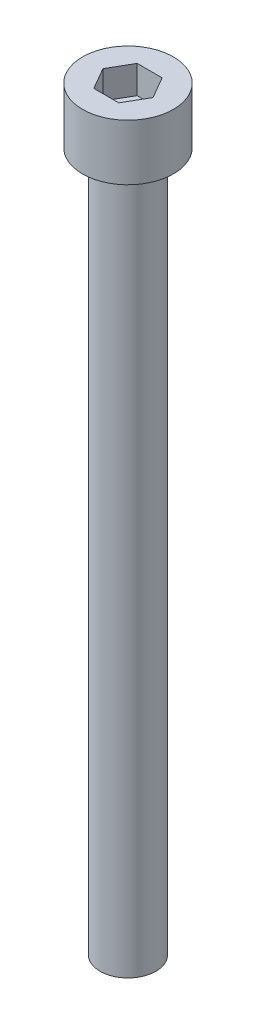
SolidWorks part; units mm, degrees
material "AISI 304"
ref_plane "前视基准面" through (0, 0, 0) normal (0, 0, 1) x (1, 0, 0)
ref_plane "上视基准面" through (0, 0, 0) normal (0, 1, 0) x (1, 0, 0)
ref_plane "右视基准面" through (0, 0, 0) normal (1, 0, 0) x (0, 0, -1)
sketch "草图1" plane through (0, 0, 0) normal (0, 1, 0) x (1, 0, 0)
  circle A0 centre (0, 0) radius 6.5
  dimension "D1" = 13
extrude "杯头" add sketch "草图1" along normal blind 8
sketch "草图2" plane through (0, 8, 0) normal (0, 1, 0) x (1, 0, 0)
  line L1 (3.5796, 0) -> (1.7898, 3.1)
  line L2 (1.7898, 3.1) -> (-1.7898, 3.1)
  line L3 (-1.7898, 3.1) -> (-3.5796, 0)
  line L4 (-3.5796, 0) -> (-1.7898, -3.1)
  line L5 (-1.7898, -3.1) -> (1.7898, -3.1)
  line L6 (1.7898, -3.1) -> (3.5796, 0)
  circle A0 centre (0, 0) radius 3.1 construction
  dimension "D1" = 6.2
extrude "内六角口" cut sketch "草图2" against normal blind 4
sketch "草图3" plane through (0, 0, 0) normal (0, -1, 0) x (1, 0, 0)
  circle A0 centre (0, 0) radius 4
  dimension "D1" = 8
extrude "螺纹长" add sketch "草图3" along normal blind 100
